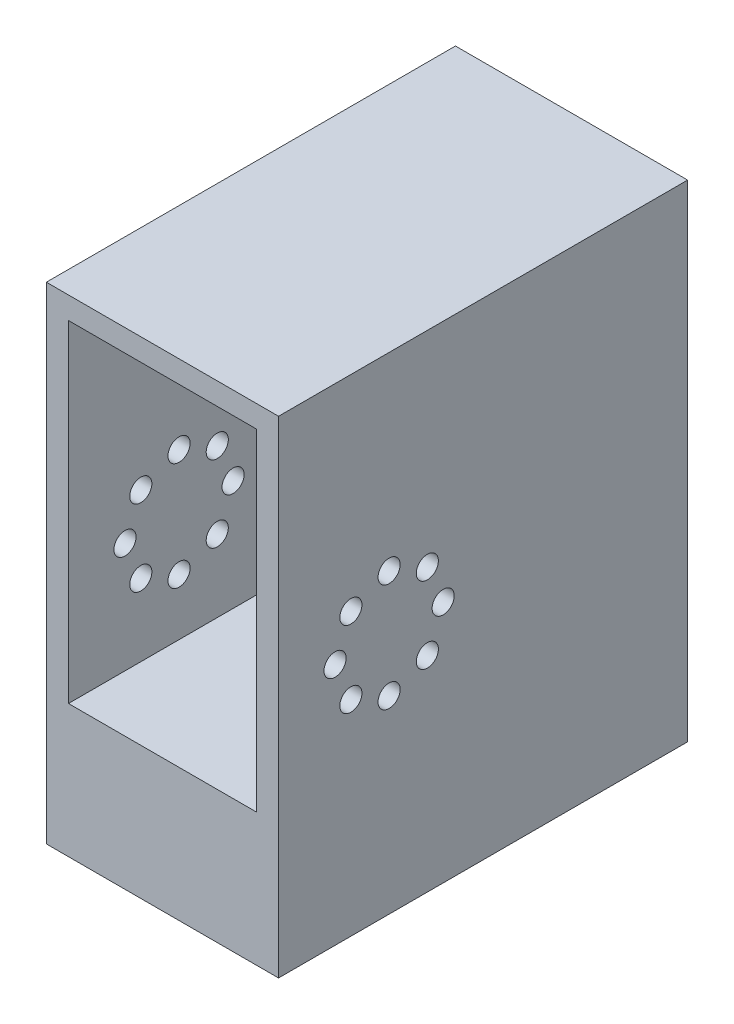
SolidWorks part; units mm, degrees
ref_plane "Alzado" through (0, 0, 0) normal (0, 0, 1) x (1, 0, 0)
ref_plane "Planta" through (0, 0, 0) normal (0, 1, 0) x (1, 0, 0)
ref_plane "Vista lateral" through (0, 0, 0) normal (1, 0, 0) x (0, 0, -1)
sketch "Croquis1" plane through (0, 0, 0) normal (0, 0, 1) x (1, 0, 0)
  line L1 (-17, -30) -> (17, -30)
  line L2 (-17, -30) -> (-17, 30)
  line L3 (-17, 30) -> (17, 30)
  line L4 (17, -30) -> (17, 30)
  line L5 (-17, -30) -> (17, 30) construction
  line L6 (-17, 30) -> (17, -30) construction
  line L7 (-21, -34) -> (21, -34)
  line L8 (-21, -34) -> (-21, 34)
  line L9 (-21, 34) -> (21, 34)
  line L10 (21, -34) -> (21, 34)
  line L11 (-21, -34) -> (21, 34) construction
  line L12 (-21, 34) -> (21, -34) construction
  point P0 (0, 0)
  point P6 (0, 0)
extrude "Saliente-Extruir1" add sketch "Croquis1" along normal blind 60
sketch "Croquis2" plane through (-17, 0, 0) normal (1, 0, 0) x (0, 0, -1)
  circle A3 centre (-49.779, -10) radius 2
  circle A4 centre (-46.9148, -3.0852) radius 2
  circle A5 centre (-40, -0.221) radius 2
  circle A6 centre (-33.0852, -3.0852) radius 2
  circle A7 centre (-30.221, -10) radius 2
  circle A8 centre (-33.0852, -16.9148) radius 2
  circle A9 centre (-40, -19.779) radius 2
  circle A10 centre (-46.9148, -16.9148) radius 2
  point P29 (-40, -10)
  dimension "D1" = 8
extrude "Cortar-Extruir1" cut sketch "Croquis2" against normal through all both and the other way through all
sketch "Croquis3" plane through (0, 0, 0) normal (0, 0, -1) x (-1, 0, 0)
  line L1 (-21, -34) -> (21, -34)
  line L2 (-21, -34) -> (-21, 34)
  line L3 (-21, 34) -> (21, 34)
  line L4 (21, -34) -> (21, 34)
extrude "Saliente-Extruir2" add sketch "Croquis3" along normal blind 4
sketch "Croquis4" plane through (21, 0, 0) normal (1, 0, 0) x (0, 0, -1)
  line L0 (-49.779, -10) -> (4, -10)
  line L1 (4, 34) -> (4, -34) construction
  line L2 (4, -34) -> (4, -54)
  line L3 (4, -54) -> (-60, -54)
  line L4 (-60, -54) -> (-60, -34)
  line L5 (-60, -34) -> (4, -34)
  line M10 (-60, -34) -> (4, -34)
extrude "Saliente-Extruir3" add sketch "Croquis4" against normal up to surface (42 mm away) contours L4 L3 L2 M10 up to face at (-21, -16.9148, 44.9148)
sketch "Croquis5" plane through (0, 0, -4) normal (0, 0, -1) x (-1, 0, 0)
  line L1 (-21, 34) -> (21, 34)
  line L2 (-21, 34) -> (-21, -54)
  line L3 (-21, -54) -> (21, -54)
  line L4 (21, 34) -> (21, -54)
  line L11 (-17, -50) -> (17, 30) construction
  line L12 (-17, 30) -> (17, -50) construction
  point P6 (0, -10)
  dimension "D1" = 42
  dimension "D2" = 88
extrude "Saliente-Extruir4" add sketch "Croquis5" along normal blind 10
sketch "Croquis6" plane through (0, 0, -14) normal (0, 0, -1) x (-1, 0, 0)
  circle A1 centre (0, -3) radius 1.2
  circle A2 centre (0, 8.6) radius 1.2
  circle A3 centre (7, -10) radius 1.2
  circle A4 centre (0, -17) radius 1.2
  circle A5 centre (-7, -10) radius 1.2
  circle A6 centre (0, -28.6) radius 1.2
extrude "Cortar-Extruir2" cut sketch "Croquis6" against normal blind 10
sketch "Croquis7" plane through (-21, 0, 0) normal (-1, 0, 0) x (0, 0, 1)
  circle A0 centre (40, -0.221) radius 2
  circle A1 centre (46.9148, -3.0852) radius 2
  circle A2 centre (49.779, -10) radius 2
  circle A3 centre (33.0852, -3.0852) radius 2
  circle A4 centre (30.221, -10) radius 2
  circle A5 centre (33.0852, -16.9148) radius 2
  circle A6 centre (40, -19.779) radius 2
  circle A7 centre (46.9148, -16.9148) radius 2
